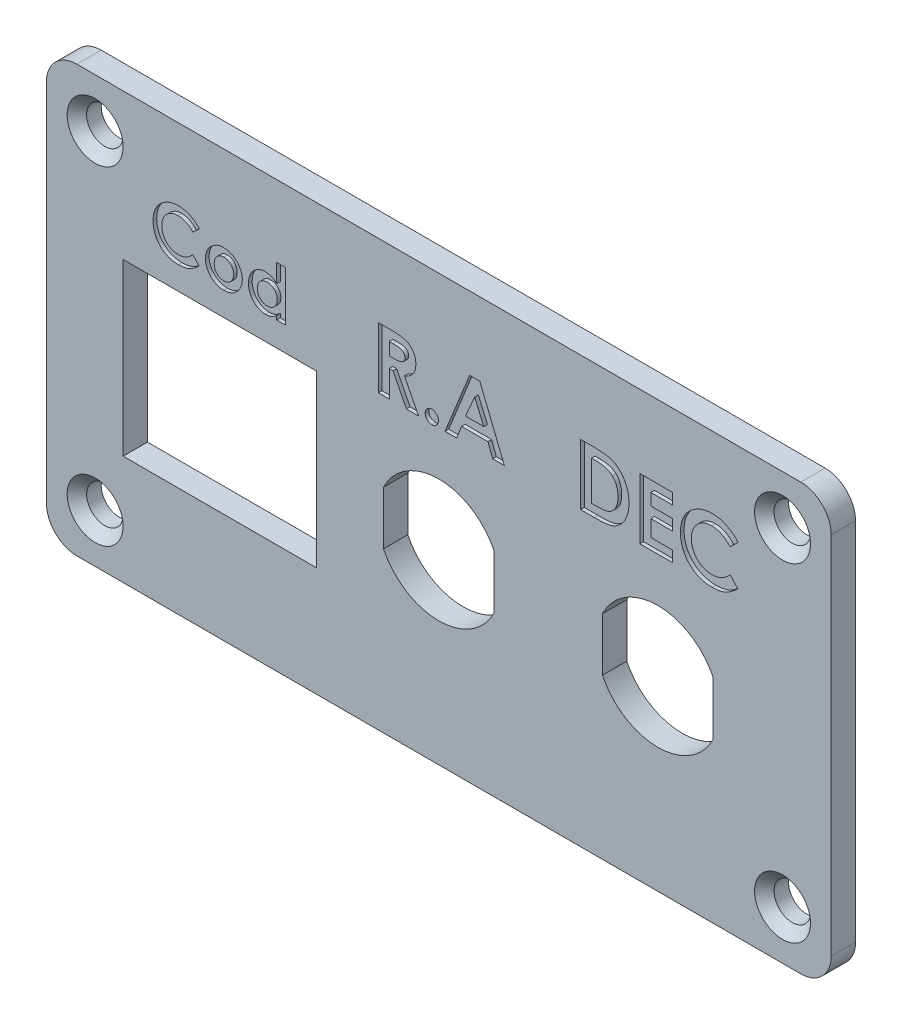
SolidWorks part; units mm, degrees
ref_plane "Plan de face" through (0, 0, 0) normal (0, 0, 1) x (1, 0, 0)
ref_plane "Plan de dessus" through (0, 0, 0) normal (0, 1, 0) x (1, 0, 0)
ref_plane "Plan de droite" through (0, 0, 0) normal (1, 0, 0) x (0, 0, -1)
sketch "Esquisse1" plane through (0, 0, 0) normal (0, 0, 1) x (1, 0, 0)
  line L0 (0, 0) -> (0, 31.7944) construction
  line L1 (-32.25, -17.5) -> (32.25, -17.5)
  line L2 (-32.25, -17.5) -> (-32.25, 17.5)
  line L3 (-32.25, 17.5) -> (32.25, 17.5)
  line L4 (32.25, -17.5) -> (32.25, 17.5)
  line L5 (-32.25, -17.5) -> (32.25, 17.5) construction
  line L6 (-32.25, 17.5) -> (32.25, -17.5) construction
  line L11 (0, -2.2) -> (18, -2.2) construction
  line L12 (-4.55, -0.0091) -> (-4.55, -4.3909)
  line L17 (-25.95, 5.5) -> (-10.05, 5.5)
  line L18 (-25.95, 5.5) -> (-25.95, -8.5)
  line L23 (-25.95, -8.5) -> (-10.05, -8.5)
  line L24 (-10.05, 5.5) -> (-10.05, -8.5)
  line L25 (0, 0) -> (22.5757, 0) construction
  line L27 (4.55, -0.0091) -> (4.55, -4.3909)
  line L28 (18, -7.5302) -> (18, -2.2) construction
  line L29 (0, -2.2) -> (0, 7.2722) construction
  line L30 (18, -2.2) -> (18, 2.3462) construction
  line L31 (13.45, -4.3909) -> (13.45, -0.0091)
  line L32 (22.55, -0.0091) -> (22.55, -4.3909)
  arc A0 (-4.55, -4.3909) -> (4.55, -4.3909) centre (0, -2.2) ccw
  circle A3 centre (28.25, 13.5) radius 1.5
  circle A4 centre (-28.25, 13.5) radius 1.5
  arc A5 (13.45, -4.3909) -> (22.55, -4.3909) centre (18, -2.2) ccw
  circle A6 centre (-28.25, -13.5) radius 1.5
  circle A7 centre (28.25, -13.5) radius 1.5
  arc A8 (4.55, -0.0091) -> (-4.55, -0.0091) centre (0, -2.2) ccw
  arc A9 (22.55, -0.0091) -> (13.45, -0.0091) centre (18, -2.2) ccw
  point P0 (0, 0)
  point P26 (15.5, -20.1)
  dimension "D4" = 3
  dimension "D7" = 27
  dimension "D8" = 10.1
  dimension "D9" = 0
  dimension "D1" = 56.5
  dimension "D2" = 64.5
  dimension "D3" = 35
  dimension "D5" = 18
  dimension "D6" = 15.3
  dimension "D10" = 15.9
  dimension "D11" = 14
  dimension "D12" = 9
  dimension "D14" = 9.1
  dimension "D15" = 9.1
extrude "Boss.-Extru.1" add sketch "Esquisse1" along normal blind 2
fillet "Congé1" radius 2.5 4 edges at (-32.25, -17.5, 1) (32.25, -17.5, 1) (32.25, 17.5, 1) (-32.25, 17.5, 1)
sketch "Esquisse2" plane through (0, 0, 2) normal (0, 0, 1) x (1, 0, 0)
  line L0 (-7.0436, 6.5) -> (7.0436, 6.5) construction
  line L1 (-29.75, -17.5) -> (29.75, -17.5) construction
  line L2 (-18, 5.5) -> (-18, 7.5) construction
  line L3 (10.5962, 6.5) -> (25.4038, 6.5) construction
  line L4 (0, 6.5) -> (0, -2.2) construction
  line L5 (18, 6.5) -> (18, -2.2) construction
  line L6 (-10.05, 5.5) -> (-25.95, 5.5) construction
  line L7 (-24.5049, 7.5) -> (-11.4951, 7.5) construction
  text T0 "<b>R.A</b>" font "Century Gothic" height 5
  text T1 "<b>DEC</b>" font "Century Gothic" height 5
  text T2 "Cod" font "Century Gothic" height 4
  point P15 (-18, 7.5)
  point P16 (-12.6031, 6.4683)
  point P19 (-24.3802, 6.5)
  point P24 (-25.5236, 6.5)
  point P25 (-24.5049, 6.5)
  dimension "D1" = 24
  dimension "D2" = 2
extrude "Texte" cut sketch "Esquisse2" against normal blind 0.3
chamfer "Chanfrein1" distance 0.8 angle 45 4 edges at (26.75, -13.5, 2) (29.75, 13.5, 2) (-26.75, 13.5, 2) (-29.75, -13.5, 2)
